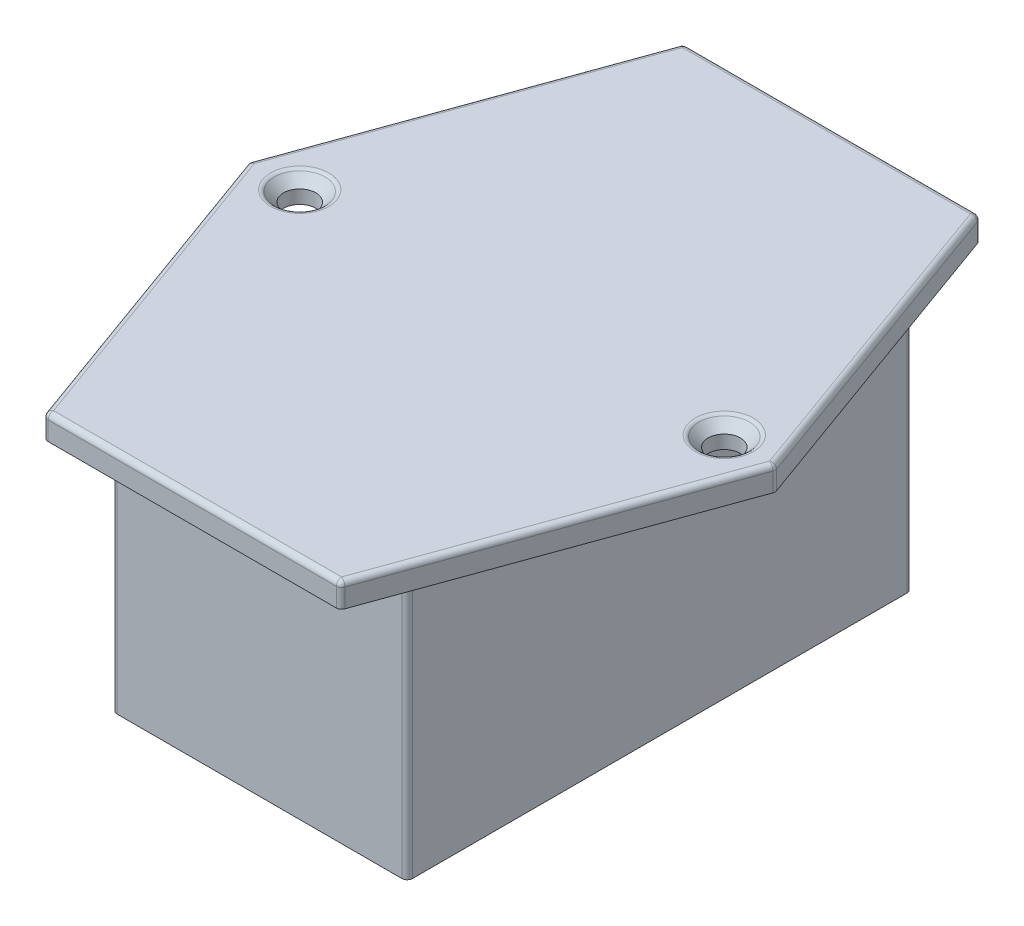
SolidWorks part; units mm, degrees
ref_plane "Front Plane" through (0, 0, 0) normal (0, 0, 1) x (1, 0, 0)
ref_plane "Top Plane" through (0, 0, 0) normal (0, 1, 0) x (1, 0, 0)
ref_plane "Right Plane" through (0, 0, 0) normal (1, 0, 0) x (0, 0, -1)
sketch "Sketch1" plane through (0, 0, 0) normal (0, 1, 0) x (1, 0, 0)
  line L1 (0, 0) -> (27.5, 0)
  line L2 (0, 0) -> (0, 47)
  line L3 (0, 47) -> (27.5, 47)
  line L4 (27.5, 0) -> (27.5, 47)
  dimension "D1" = 27.5
  dimension "D2" = 47
extrude "Boss-Extrude1" add sketch "Sketch1" along normal blind 25
sketch "Sketch2" plane through (0, 25, 0) normal (0, 1, 0) x (1, 0, 0)
  line L0 (0, 53.25) -> (27.5, 53.25)
  line L1 (27.5, 53.25) -> (38.25, 23.5)
  line L2 (38.25, 23.5) -> (27.5, -6.25)
  line L3 (27.5, -6.25) -> (0, -6.25)
  line L4 (0, -6.25) -> (-10.75, 23.5)
  line L5 (-10.75, 23.5) -> (0, 53.25)
  line L6 (-10.75, 23.5) -> (38.25, 23.5) construction
  line L7 (13.75, 53.25) -> (13.75, -6.25) construction
  line L8 (0, 0) -> (27.5, 0) construction
  line L9 (0, 47) -> (27.5, 0) construction
  circle A0 centre (-6, 23.5) radius 1.5
  circle A1 centre (33.5, 23.5) radius 1.5
  point P8 (13.75, 23.5)
  dimension "D5" = 3
  dimension "D1" = 59.5
  dimension "D2" = 49
  dimension "D3" = 19.75
  dimension "D4" = 19.75
extrude "Boss-Extrude2" add sketch "Sketch2" along normal blind 2.25
chamfer "Chamfer1" distance 1 angle 45 2 edges at (-6, 27.25, -22) (33.5, 27.25, -22)
fillet "Fillet1" radius 0.5 18 edges at (13.75, 27.25, -53.25) (32.875, 27.25, -38.375) (32.875, 27.25, -8.625) (13.75, 27.25, 6.25) (-5.375, 27.25, -8.625) (-5.375, 27.25, -38.375) (-10.75, 26.125, -23.5) (0, 12.5, -47) (0, 12.5, 0) (27.5, 12.5, 0) (27.5, 12.5, -47) (0, 26.125, -53.25) (27.5, 26.125, -53.25) (38.25, 26.125, -23.5) (27.5, 26.125, 6.25) (0, 26.125, 6.25) (33.5, 27.25, -26) (-6, 27.25, -26)
